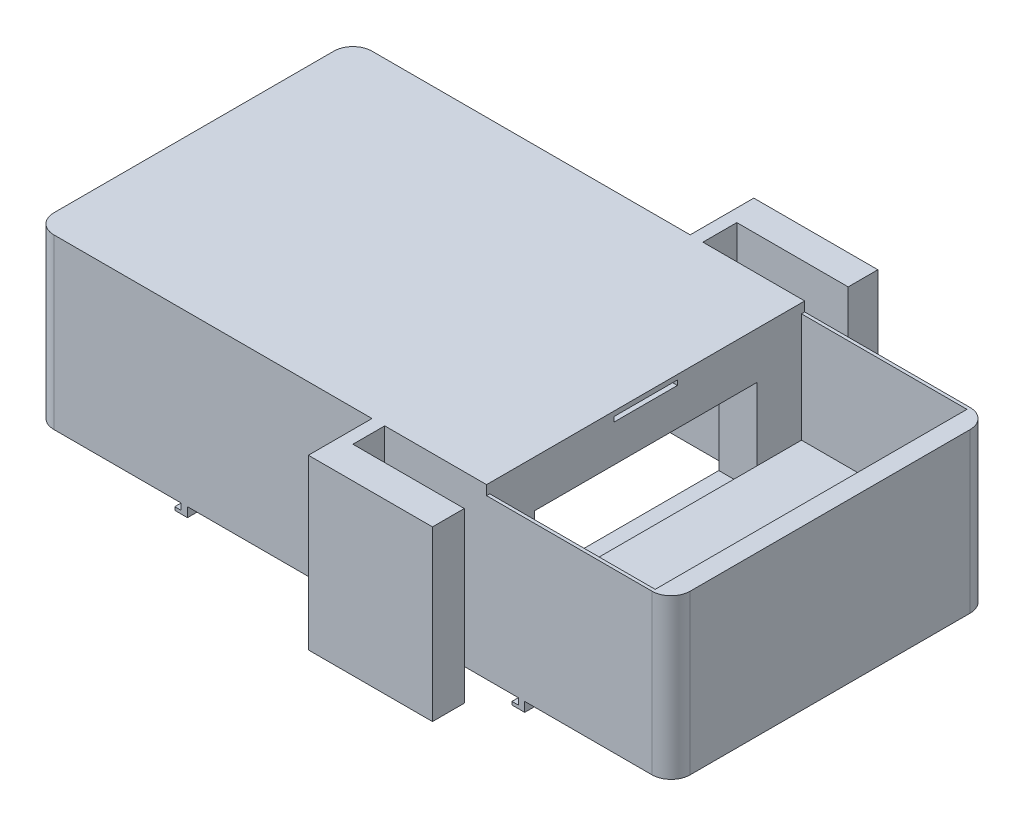
SolidWorks part; units mm, degrees
ref_plane "Front Plane" through (0, 0, 0) normal (0, 0, 1) x (1, 0, 0)
ref_plane "Top Plane" through (0, 0, 0) normal (0, 1, 0) x (1, 0, 0)
ref_plane "Right Plane" through (0, 0, 0) normal (1, 0, 0) x (0, 0, -1)
sketch "Sketch2" plane through (0, 0, 0) normal (0, 1, 0) x (1, 0, 0)
  line L1 (47, -25) -> (-47, -25)
  line L2 (50, -22) -> (50, 22)
  line L3 (47, 25) -> (-47, 25)
  line L4 (-50, -22) -> (-50, 22)
  line L5 (50, -25) -> (-50, 25) construction
  line L6 (50, 25) -> (-50, -25) construction
  arc A0 (-47, 25) -> (-50, 22) centre (-47, 22) ccw
  arc A1 (-47, -25) -> (-50, -22) centre (-47, -22) cw
  arc A2 (50, -22) -> (47, -25) centre (47, -22) cw
  arc A3 (50, 22) -> (47, 25) centre (47, 22) ccw
  point P0 (0, 0)
  dimension "D3" = 3
  dimension "D4" = 3
  dimension "D5" = 3
  dimension "D6" = 3
  dimension "D1" = 100
  dimension "D2" = 50
extrude "Boss-Extrude1" add sketch "Sketch2" along normal blind 25
sketch "Sketch3" plane through (0, 25, 0) normal (0, 1, 0) x (1, 0, 0)
  line L0 (47, 25) -> (-47, 25) construction
  line L1 (21, 24.5) -> (47, 24.5)
  line L2 (21, 24.5) -> (21, -24.5)
  line L3 (21, -24.5) -> (47, -24.5)
  line L4 (47, 24.5) -> (47, -24.5)
  line L5 (-50, 22) -> (-50, -22) construction
  dimension "D1" = 26
  dimension "D2" = 49
  dimension "D3" = 0.5
  dimension "D4" = 71
extrude "Cut-Extrude1" cut sketch "Sketch3" against normal blind 17.2
sketch "Sketch4" plane through (0, 0, 0) normal (0, -1, 0) x (1, 0, 0)
  line L0 (-47, 25) -> (47, 25) construction
  line L1 (-47, 23) -> (15, 23)
  line L2 (-47, 23) -> (-47, -23)
  line L3 (-47, -23) -> (15, -23)
  line L4 (15, 23) -> (15, -23)
  line L5 (-50, -22) -> (-50, 22) construction
  line L6 (47, -25) -> (-47, -25) construction
  dimension "D1" = 2
  dimension "D2" = 3
  dimension "D3" = 2
  dimension "D4" = 65
extrude "Cut-Extrude2" cut sketch "Sketch4" against normal blind 22
sketch "Sketch5" plane through (-50, 0, 0) normal (-1, 0, 0) x (0, 0, 1)
  line L0 (22, 25) -> (22, 0) construction
  line L1 (-9.75, 22.5) -> (-7.75, 22.5)
  line L2 (-9.75, 22.5) -> (-9.75, 2.5)
  line L3 (-9.75, 2.5) -> (-7.75, 2.5)
  line L4 (-7.75, 22.5) -> (-7.75, 2.5)
  line L5 (-6.25, 22.5) -> (-4.25, 22.5)
  line L6 (-6.25, 22.5) -> (-6.25, 2.5)
  line L7 (-6.25, 2.5) -> (-4.25, 2.5)
  line L8 (-4.25, 22.5) -> (-4.25, 2.5)
  line L9 (-2.75, 22.5) -> (-0.75, 22.5)
  line L10 (-2.75, 22.5) -> (-2.75, 2.5)
  line L11 (-2.75, 2.5) -> (-0.75, 2.5)
  line L12 (-0.75, 22.5) -> (-0.75, 2.5)
  line L13 (0.75, 22.5) -> (2.75, 22.5)
  line L14 (0.75, 22.5) -> (0.75, 2.5)
  line L15 (0.75, 2.5) -> (2.75, 2.5)
  line L16 (2.75, 22.5) -> (2.75, 2.5)
  line L17 (4.25, 22.5) -> (6.25, 22.5)
  line L18 (4.25, 22.5) -> (4.25, 2.5)
  line L19 (4.25, 2.5) -> (6.25, 2.5)
  line L20 (6.25, 22.5) -> (6.25, 2.5)
  line L21 (7.75, 22.5) -> (9.75, 22.5)
  line L22 (7.75, 22.5) -> (7.75, 2.5)
  line L23 (-22, 25) -> (-22, 0) construction
  line L24 (7.75, 2.5) -> (9.75, 2.5)
  line L25 (9.75, 22.5) -> (9.75, 2.5)
  line L26 (-22, 25) -> (22, 25) construction
  line L27 (-22, 0) -> (22, 0) construction
  dimension "D1" = 12.25
  dimension "D2" = 2
  dimension "D3" = 3.5
  dimension "D4" = 2
  dimension "D5" = 1.5
  dimension "D6" = 1.5
  dimension "D7" = 1.5
  dimension "D8" = 12.25
  dimension "D9" = 2
  dimension "D10" = 2
  dimension "D11" = 2
  dimension "D12" = 1.5
  dimension "D13" = 2
  dimension "D14" = 20
  dimension "D15" = 20
  dimension "D16" = 20
  dimension "D17" = 20
  dimension "D18" = 20
  dimension "D19" = 20
  dimension "D20" = 2.5
  dimension "D21" = 2.5
  dimension "D22" = 2.5
  dimension "D23" = 2.5
  dimension "D24" = 2.5
  dimension "D25" = 2.5
extrude "Cut-Extrude4" cut sketch "Sketch5" against normal blind 3
sketch "Sketch6" plane through (0, 0, -25) normal (0, 0, -1) x (-1, 0, 0)
  line L0 (-47, 25) -> (-47, 0) construction
  line L1 (22, 22.6011) -> (45, 22.6011)
  line L2 (22, 22.6011) -> (22, 7.6011)
  line L3 (22, 7.6011) -> (45, 7.6011)
  line L4 (45, 22.6011) -> (45, 7.6011)
  dimension "D1" = 23
  dimension "D2" = 15
  dimension "D3" = 69
extrude "Cut-Extrude5" cut sketch "Sketch6" against normal blind 2
sketch "Sketch7" plane through (15, 0, 0) normal (-1, 0, 0) x (0, 0, 1)
  line L0 (23, 22) -> (23, 0) construction
  line L1 (17.5, 4.169) -> (-17.5, 4.169)
  line L2 (17.5, 4.169) -> (17.5, 19.169)
  line L3 (17.5, 19.169) -> (-17.5, 19.169)
  line L4 (-17.5, 4.169) -> (-17.5, 19.169)
  dimension "D1" = 35
  dimension "D2" = 15
  dimension "D3" = 5.5
extrude "Cut-Extrude6" cut sketch "Sketch7" against normal blind 6
sketch "Sketch8" plane through (0, 25, 0) normal (0, 1, 0) x (1, 0, 0)
  line L0 (47, 25) -> (-47, 25) construction
  line L1 (-47, 25) -> (21, 25)
  line L2 (-50, 22) -> (-50, -22)
  line L3 (-47, -25) -> (21, -25)
  line L4 (21, 25) -> (21, -25)
  line L9 (-50, 22) -> (-50, -22) construction
  line L10 (-47, -25) -> (47, -25) construction
  line L11 (21, 24.5) -> (21, -24.5) construction
  arc A0 (-50, 22) -> (-47, 25) centre (-47, 22) cw
  arc A1 (-47, -25) -> (-50, -22) centre (-47, -22) cw
  dimension "D1" = 3
  dimension "D2" = 3
extrude "Boss-Extrude2" add sketch "Sketch8" along normal blind 1.5
sketch "Sketch9" plane through (21, 0, 0) normal (1, 0, 0) x (0, 0, -1)
  line L0 (-22, 25) -> (22, 25) construction
  line L1 (-5, 25.75) -> (5, 25.75)
  line L2 (-5, 25.75) -> (-5, 25)
  line L3 (-5, 25) -> (5, 25)
  line L4 (5, 25.75) -> (5, 25)
  line L5 (-25, 26.5) -> (-25, 25) construction
  dimension "D1" = 0.75
  dimension "D2" = 10
  dimension "D3" = 20
extrude "Cut-Extrude7" cut sketch "Sketch9" against normal blind 7.5
sketch "Sketch10" plane through (0, 0, 0) normal (0, -1, 0) x (1, 0, 0)
  line L0 (15, 23) -> (-47, 23) construction
  line L1 (-27, 25) -> (-26, 25)
  line L2 (-27, 25) -> (-27, 23)
  line L3 (-27, 23) -> (-26, 23)
  line L4 (-26, 25) -> (-26, 23)
  line L5 (29, 24.8758) -> (30, 24.8758)
  line L6 (29, 24.8758) -> (29, 22.8758)
  line L7 (29, 22.8758) -> (30, 22.8758)
  line L8 (30, 24.8758) -> (30, 22.8758)
  line L9 (-47, 23) -> (-47, -23) construction
  line L10 (50, 22) -> (50, -22) construction
  dimension "D1" = 2
  dimension "D2" = 0
  dimension "D3" = 1
  dimension "D4" = 2
  dimension "D5" = 1
  dimension "D6" = 20
  dimension "D7" = 20
extrude "Boss-Extrude3" add sketch "Sketch10" along normal blind 1.5 contours L2 L1 L4 L3
sketch "Sketch11" plane through (0, 0, 0) normal (0, -1, 0) x (1, 0, 0)
  line L0 (47, -25) -> (-47, -25) construction
  line L1 (-27, -23) -> (-26, -23)
  line L2 (-27, -23) -> (-27, -25)
  line L3 (-27, -25) -> (-26, -25)
  line L4 (-26, -23) -> (-26, -25)
  line L5 (-50, -22) -> (-50, 22) construction
  line L6 (50, 22) -> (50, -22) construction
  line L7 (-26, 25) -> (47, 25) construction
  line L8 (26, 25) -> (27, 25)
  line L9 (26, 25) -> (26, 23)
  line L10 (26, 23) -> (27, 23)
  line L11 (27, 25) -> (27, 23)
  line L13 (26, -23) -> (27, -23)
  line L14 (26, -23) -> (26, -25)
  line L15 (26, -25) -> (27, -25)
  line L16 (27, -23) -> (27, -25)
  dimension "D1" = 2
  dimension "D2" = 1
  dimension "D3" = 23
  dimension "D4" = 1
  dimension "D5" = 2
  dimension "D6" = 23
  dimension "D7" = 1
  dimension "D8" = 2
  dimension "D9" = 23
extrude "Boss-Extrude4" add sketch "Sketch11" along normal blind 1.5
sketch "Sketch12" plane through (-27, 0, 0) normal (-1, 0, 0) x (0, 0, 1)
  line L0 (23, -1.5) -> (23, 0) construction
  line L1 (23, -1) -> (25, -1)
  line L2 (23, -1) -> (23, -1.5)
  line L3 (23, -1.5) -> (25, -1.5)
  line L4 (25, -1) -> (25, -1.5)
  line L6 (25, -1.5) -> (23, -1.5) construction
  dimension "D1" = 0.5
  dimension "D2" = 2
extrude "Boss-Extrude5" add sketch "Sketch12" along normal blind 1
sketch "Sketch13" plane through (-27, 0, 0) normal (-1, 0, 0) x (0, 0, 1)
  line L0 (-25, -1.5) -> (-25, 0) construction
  line L1 (-25, -1) -> (-23, -1)
  line L2 (-25, -1) -> (-25, -1.5)
  line L3 (-25, -1.5) -> (-23, -1.5)
  line L4 (-23, -1) -> (-23, -1.5)
  line L5 (-23, -1.5) -> (-25, -1.5) construction
  point P8 (-24, -1.5)
  dimension "D1" = 2
  dimension "D2" = 0.5
  dimension "D3" = 0
  dimension "D4" = 0
extrude "Boss-Extrude6" add sketch "Sketch13" along normal blind 1
sketch "Sketch14" plane through (26, 0, 0) normal (-1, 0, 0) x (0, 0, 1)
  line L1 (-25, -1) -> (-23, -1)
  line L2 (-25, -1) -> (-25, -1.5)
  line L3 (-25, -1.5) -> (-23, -1.5)
  line L4 (-23, -1) -> (-23, -1.5)
  line L5 (-25, -1.5) -> (-25, 0) construction
  line L7 (-23, -1.5) -> (-25, -1.5) construction
  dimension "D1" = 2
  dimension "D2" = 0.5
  dimension "D3" = 0
  dimension "D4" = 0
extrude "Boss-Extrude7" add sketch "Sketch14" along normal blind 1
sketch "Sketch15" plane through (26, 0, 0) normal (-1, 0, 0) x (0, 0, 1)
  line L0 (23, -1.5) -> (23, 0) construction
  line L1 (23, -1) -> (25, -1)
  line L2 (23, -1) -> (23, -1.5)
  line L3 (23, -1.5) -> (25, -1.5)
  line L4 (25, -1) -> (25, -1.5)
  line L5 (25, -1.5) -> (23, -1.5) construction
  dimension "D1" = 2
  dimension "D2" = 0.5
  dimension "D3" = 0
  dimension "D4" = 0
extrude "Boss-Extrude8" add sketch "Sketch15" along normal blind 1
sketch "Sketch17" plane through (0, 0, 25) normal (0, 0, 1) x (1, 0, 0)
  line L0 (-47, 26.5) -> (-47, 0) construction
  line L1 (3, 26.5) -> (5, 26.5)
  line L2 (3, 26.5) -> (3, 0)
  line L3 (3, 0) -> (5, 0)
  line L4 (5, 26.5) -> (5, 0)
  line L5 (-47, 26.5) -> (21, 26.5) construction
  line L6 (-26, 0) -> (26, 0) construction
  dimension "D1" = 50
  dimension "D2" = 2
extrude "Boss-Extrude10" add sketch "Sketch17" along normal blind 10
sketch "Sketch18" plane through (0, 0, -25) normal (0, 0, -1) x (-1, 0, 0)
  line L0 (47, 26.5) -> (47, 0) construction
  line L1 (-3, 0) -> (-5, 0)
  line L2 (-3, 0) -> (-3, 26.5)
  line L3 (-3, 26.5) -> (-5, 26.5)
  line L4 (-5, 0) -> (-5, 26.5)
  line L5 (-21, 26.5) -> (47, 26.5) construction
  line L6 (-26, 0) -> (26, 0) construction
  dimension "D1" = 50
  dimension "D2" = 2
extrude "Boss-Extrude11" add sketch "Sketch18" along normal blind 10
sketch "Sketch19" plane through (5, 0, 0) normal (1, 0, 0) x (0, 0, -1)
  line L0 (35, 26.5) -> (35, 0) construction
  line L1 (-35, 26.5) -> (-30, 26.5)
  line L2 (-35, 26.5) -> (-35, 0)
  line L3 (-35, 0) -> (-30, 0)
  line L4 (-30, 26.5) -> (-30, 0)
  line L5 (30.3322, 26.5) -> (35, 26.5)
  line L6 (30.3322, 26.5) -> (30.3322, 0)
  line L7 (30.3322, 0) -> (35, 0)
  line L8 (35, 26.5) -> (35, 0)
  line L9 (35, 26.5) -> (25, 26.5) construction
  line L10 (35, 0) -> (25, 0) construction
  line L11 (-35, 26.5) -> (-25, 26.5) construction
  line L12 (-35, 0) -> (-25, 0) construction
  line L13 (-35, 0) -> (-35, 26.5) construction
  dimension "D1" = 5
extrude "Boss-Extrude13" add sketch "Sketch19" along normal blind 17.5
sketch "Sketch20" plane through (0, 22, 0) normal (0, -1, 0) x (1, 0, 0)
  circle A0 centre (-40.5, 11.075) radius 2.5
  circle A1 centre (8.5, 11.075) radius 2.5
  circle A2 centre (-40.5, -11.075) radius 2.5
  circle A3 centre (8.5, -11.075) radius 2.5
  dimension "D5" = 5
  dimension "D6" = 5
  dimension "D7" = 5
  dimension "D8" = 5
  dimension "D11" = 22.15
extrude "Boss-Extrude14" add sketch "Sketch20" along normal blind 7
sketch "Sketch21" plane through (0, 15, 0) normal (0, -1, 0) x (-1, 0, 0)
  line L0 (-15, 23) -> (-15, -23) construction
  circle A0 centre (-8.5, 11.075) radius 1.5
  circle A1 centre (-8.5, 11.075) radius 2.5 construction
  circle A2 centre (-8.5, -11.075) radius 1.5
  circle A3 centre (-8.5, -11.075) radius 2.5 construction
  circle A4 centre (40.5, 11.075) radius 1.5
  circle A5 centre (40.5, 11.075) radius 2.5 construction
  circle A6 centre (40.5, -11.075) radius 1.5
  circle A7 centre (40.5, -11.075) radius 2.5 construction
  dimension "D1" = 3
  dimension "D3" = 0
  dimension "D4" = 3
  dimension "D5" = 0
  dimension "D6" = 3
  dimension "D7" = 0
  dimension "D8" = 3
  dimension "D9" = 0
  dimension "D2" = 4
extrude "Cut-Extrude8" cut sketch "Sketch21" against normal blind 5
